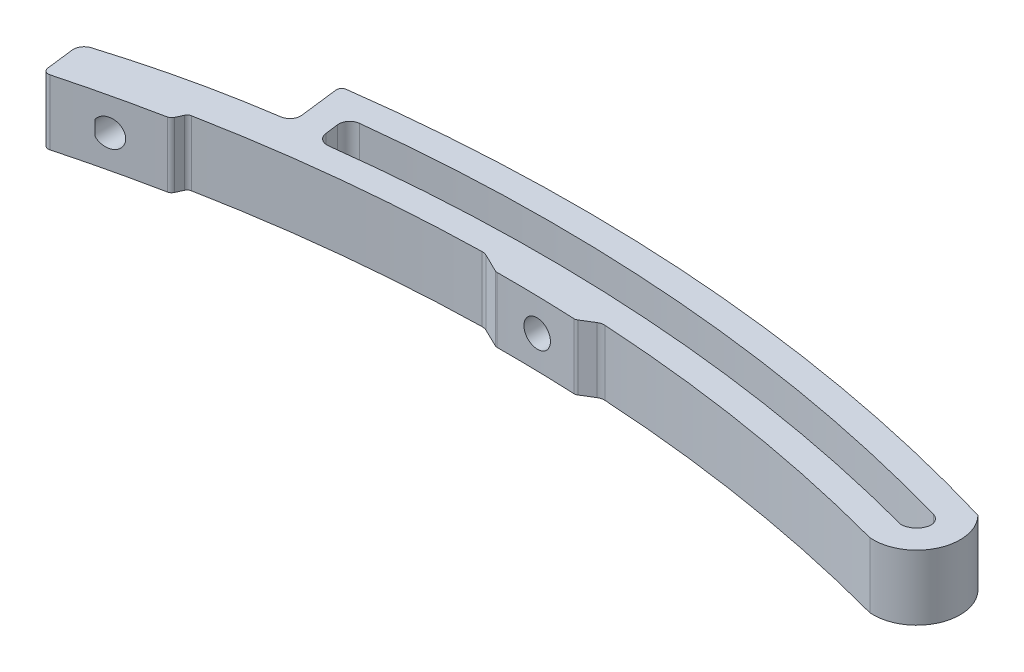
SolidWorks part; units mm, degrees
ref_plane "Front Plane" through (0, 0, 0) normal (0, 0, 1) x (1, 0, 0)
ref_plane "Top Plane" through (0, 0, 0) normal (0, 1, 0) x (1, 0, 0)
ref_plane "Right Plane" through (0, 0, 0) normal (1, 0, 0) x (0, 0, -1)
sketch "Sketch2" plane through (0, 0, 0) normal (0, 1, 0) x (1, 0, 0)
  line L0 (0, 0) -> (151, 0) construction
  line L1 (0, 0) -> (-0.7312, 5.9553)
  line L3 (0, 0) -> (-50000, 0) construction
  line L4 (31.3208, 13.1684) -> (30.0877, 23.2105)
  line L5 (0, 0) -> (151, 0) construction
  arc A0 (157.4172, 13.558) -> (151, 0) centre (151.6924, 7.97) cw
  arc A1 (0, 0) -> (151, 0) centre (75.5, -280.0125) cw
  arc A2 (157.4172, 13.558) -> (30.0877, 23.2105) centre (71.3382, -277.2907) ccw
  arc A4 (31.3208, 13.1684) -> (-0.7312, 5.9553) centre (56.9124, -175.37) ccw
  point P5 (75.5, 10)
  point P6 (75.5, 26)
  point P9 (75.5, 0)
  point P14 (0, 0)
  point P16 (151.6924, 7.97)
  dimension "D3" = 8
  dimension "D4" = 97
  dimension "D6" = 97
  dimension "D12" = 190.2673
  dimension "D1" = 151
  dimension "D2" = 15
  dimension "D5" = 38
  dimension "D7" = 158
  dimension "D8" = 10
  dimension "D9" = 26
  dimension "D10" = 51
  dimension "D11" = 46.1
  dimension "D13" = 6
extrude "Boss-Extrude1" add sketch "Sketch2" along normal blind 12
fillet "Fillet4" radius 1 1 edges at (30.0877, 6, -23.2105)
fillet "Fillet5" radius 2 1 edges at (31.3208, 6, -13.1684)
fillet "Fillet6" radius 2 1 edges at (-0.7312, 6, -5.9553)
sketch "Sketch5" plane through (0, 0, 0) normal (0, 1, 0) x (1, 0, 0)
  line L2 (-0.5281, 4.3009) -> (0, 0)
  line L3 (30.2081, 22.2304) -> (31.0814, 15.1183)
  line L4 (-0.5281, 4.3009) -> (0, 0)
  line L5 (30.2081, 22.2304) -> (31.0814, 15.1183)
  line L8 (35.6562, 18.8869) -> (36.4521, 12.4044)
  line L9 (35.6562, 18.8869) -> (36.4521, 12.4044)
  arc A4 (153.1906, 9.5796) -> (154.541, 7.029) centre (152.6419, 7.6563) cw
  arc A7 (29.3856, 12.8956) -> (0.8679, 6.4559) centre (56.9124, -175.37) ccw
  arc A8 (0.8679, 6.4559) -> (-0.5281, 4.3009) centre (1.457, 4.5446) ccw
  arc A9 (151, 0) -> (0, 0) centre (75.5, -280.0125) ccw
  arc A10 (151, 0) -> (157.4172, 13.558) centre (151.6924, 7.97) ccw
  arc A11 (157.4172, 13.558) -> (31.0679, 23.3434) centre (71.3382, -277.2907) ccw
  arc A12 (31.0679, 23.3434) -> (30.2081, 22.2304) centre (31.2006, 22.3523) ccw
  arc A13 (29.3856, 12.8956) -> (31.0814, 15.1183) centre (29.0963, 14.8745) ccw
  arc A14 (29.3856, 12.8956) -> (0.8679, 6.4559) centre (56.9124, -175.37) ccw
  arc A15 (0.8679, 6.4559) -> (-0.5281, 4.3009) centre (1.457, 4.5446) ccw
  arc A16 (151, 0) -> (0, 0) centre (75.5, -280.0125) ccw
  arc A17 (151, 0) -> (157.4172, 13.558) centre (151.6924, 7.97) ccw
  arc A18 (157.4172, 13.558) -> (31.0679, 23.3434) centre (71.3382, -277.2907) ccw
  arc A19 (31.0679, 23.3434) -> (30.2081, 22.2304) centre (31.2006, 22.3523) ccw
  arc A20 (29.3856, 12.8956) -> (31.0814, 15.1183) centre (29.0963, 14.8745) ccw
  arc A22 (154.4163, 9.227) -> (35.6562, 18.8869) centre (71.3382, -277.2907) ccw
  arc A23 (151.768, 4.9709) -> (154.4163, 9.227) centre (151.6924, 7.97) ccw
  arc A24 (151.768, 4.9709) -> (36.4521, 12.4044) centre (75.5, -280.0125) ccw
  arc A25 (153.1906, 9.5796) -> (35.6562, 18.8869) centre (71.3382, -277.2907) ccw
  arc A26 (151.768, 4.9709) -> (154.541, 7.029) centre (151.6924, 7.97) ccw
  arc A27 (151.768, 4.9709) -> (36.4521, 12.4044) centre (75.5, -280.0125) ccw
  dimension "D3" = 2
  dimension "D1" = 0
  dimension "D2" = 5
extrude "Cut-Extrude3" cut sketch "Sketch5" along normal blind 33 contours A25 L9 A27 A26 A4
fillet "Fillet8" radius 2 2 edges at (36.4521, 6, -12.4044) (35.6562, 6, -18.8869)
sketch "Sketch6" plane through (0, 0, 0) normal (0, 1, 0) x (1, 0, 0)
  line L0 (0, 0) -> (0.2437, -1.9851)
  line L1 (19.4605, 2.5159) -> (20.4605, 4.7293)
  line L2 (-0.5281, 4.3009) -> (0, 0) construction
  arc A0 (151, 0) -> (0, 0) centre (75.5, -280.0125) ccw construction
  arc A1 (0.2437, -1.9851) -> (19.4605, 2.5159) centre (75.5, -280.0125) cw
  arc A2 (0, 0) -> (20.4605, 4.7293) centre (75.5, -280.0125) cw
  point P0 (20.4605, 4.7293)
  dimension "D1" = 21
  dimension "D2" = 2
  dimension "D3" = 1
extrude "Boss-Extrude2" add sketch "Sketch6" along normal blind 12
fillet "Fillet9" radius 1 1 edges at (0.2437, 6, 1.9851)
fillet "Fillet10" radius 1 2 edges at (20.4605, 6, -4.7293) (19.4605, 6, -2.5159)
sketch "Sketch7" plane through (0, 0, 0) normal (0, 1, 0) x (1, 0, 0)
  line L0 (70, 9.9478) -> (74, 7.9961)
  line L1 (89, 7.6834) -> (92, 9.5302)
  arc A0 (151, 0) -> (20.9704, 4.8274) centre (75.5, -280.0125) ccw construction
  arc A1 (74, 7.9961) -> (89, 7.6834) centre (75.5, -280.0125) cw
  arc A2 (70, 9.9478) -> (92, 9.5302) centre (75.5, -280.0125) cw
  point P0 (70, 9.9478)
  dimension "D3" = 2
  dimension "D1" = 70
  dimension "D2" = 22
  dimension "D4" = 4
  dimension "D5" = 3
extrude "Boss-Extrude3" add sketch "Sketch7" along normal blind 12
fillet "Fillet11" radius 2 1 edges at (70, 6, -9.9478)
fillet "Fillet12" radius 1 2 edges at (89, 6, -7.6834) (74, 6, -7.9961)
fillet "Fillet13" radius 2 1 edges at (92, 6, -9.5302)
sketch "Sketch10" plane through (0, 0, 0) normal (0, 0, 1) x (1, 0, 0)
  line L0 (88.6925, 0) -> (88.6925, 12) construction
  line L1 (74.2331, 0) -> (88.6925, 0) construction
  line L2 (0.1035, 0) -> (0.1035, 12) construction
  circle A0 centre (81.6925, 6) radius 2.5
  circle A1 centre (10.1035, 6) radius 2.5
  dimension "D1" = 5
  dimension "D2" = 7
  dimension "D3" = 6
  dimension "D4" = 10
extrude "Cut-Extrude4" cut sketch "Sketch10" against normal blind 18
